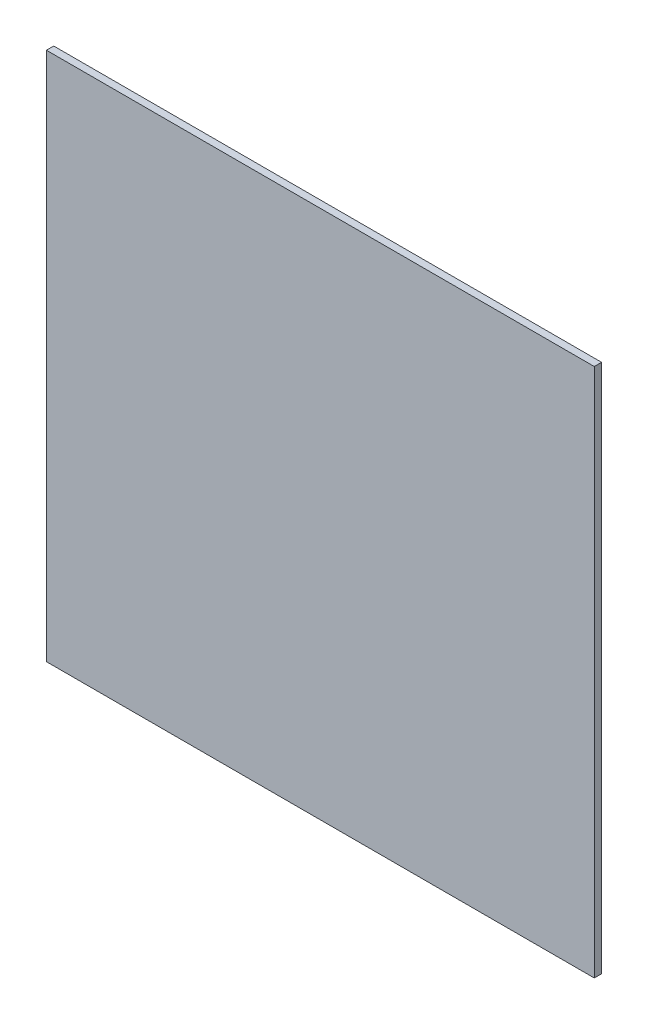
SolidWorks part; units mm, degrees
ref_plane "Front Plane" through (0, 0, 0) normal (0, 0, 1) x (1, 0, 0)
ref_plane "Top Plane" through (0, 0, 0) normal (0, 1, 0) x (1, 0, 0)
ref_plane "Right Plane" through (0, 0, 0) normal (1, 0, 0) x (0, 0, -1)
sketch "Sketch1" plane through (0, 0, 0) normal (0, 0, 1) x (1, 0, 0)
  line L1 (0, 0) -> (300, 0)
  line L2 (0, 0) -> (0, 300)
  line L3 (0, 300) -> (300, 300)
  line L4 (300, 0) -> (300, 300)
  dimension "D1" = 300
  dimension "D2" = 300
extrude "Boss-Extrude1" add sketch "Sketch1" along normal blind 4
sketch "Sketch2" plane through (0, 0, 0) normal (0, -1, 0) x (-1, 0, 0)
  line L0 (0, -4) -> (0, 0) construction
  line L1 (-150, 0) -> (-150, -5.8248) construction
  line L2 (0, 0) -> (-300, 0) construction
  circle A0 centre (-50, -2) radius 1.5
  circle A1 centre (-250, -2) radius 1.5
  circle A2 centre (-150, -2) radius 1.5
  point P4 (0, -2)
  dimension "D1" = 3
  dimension "D2" = 200
extrude "Cut-Extrude1" cut sketch "Sketch2" against normal blind 25
sketch "Sketch3" plane through (0, 0, 0) normal (0, 0, -1) x (-1, 0, 0)
  line L0 (0, 300) -> (0, 0) construction
  line L1 (0, 300) -> (-300, 300)
  line L2 (0, 300) -> (0, 290)
  line L3 (0, 290) -> (-300, 290)
  line L4 (-300, 300) -> (-300, 290)
  line L5 (-300, 300) -> (0, 300) construction
  line L6 (-300, 0) -> (-300, 300) construction
  dimension "D1" = 10
extrude "Cut-Extrude2" cut sketch "Sketch3" against normal through all
sketch "Sketch4" plane through (0, 0, 0) normal (-1, 0, 0) x (0, 0, 1)
  line L0 (4, 290) -> (0, 290) construction
  line L1 (0, 145) -> (16.7355, 145) construction
  line L2 (0, 290) -> (0, 0) construction
  circle A0 centre (2, 245) radius 1.5
  circle A1 centre (2, 45) radius 1.5
  circle A2 centre (2, 145) radius 1.5
  point P5 (2, 290)
  point P13 (0, 0)
  dimension "D1" = 3
  dimension "D2" = 200
extrude "Cut-Extrude3" cut sketch "Sketch4" against normal blind 25
